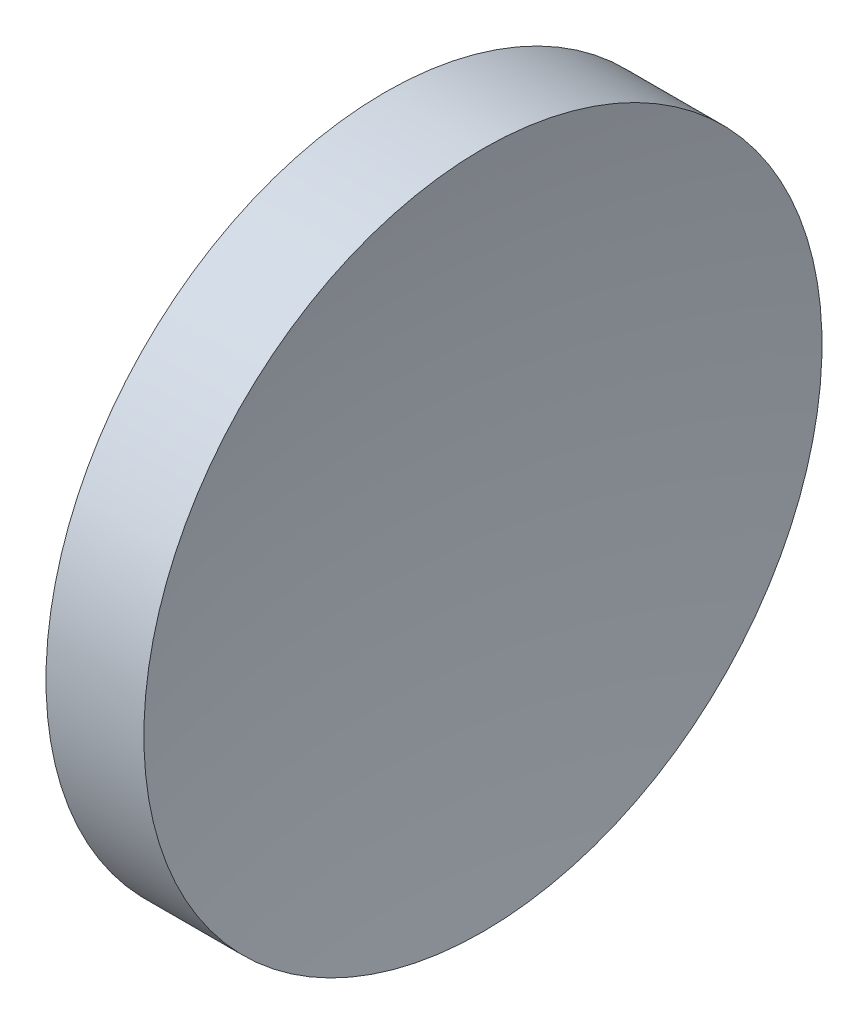
SolidWorks part; units mm, degrees
ref_plane "前视基准面" through (0, 0, 0) normal (0, 0, 1) x (1, 0, 0)
ref_plane "上视基准面" through (0, 0, 0) normal (0, 1, 0) x (1, 0, 0)
ref_plane "右视基准面" through (0, 0, 0) normal (1, 0, 0) x (0, 0, -1)
sketch "草图1" plane through (0, 0, 0) normal (0, 0, 1) x (1, 0, 0)
  line L0 (110.0148, 65.1575) -> (128.1887, 65.1575) construction
  line L1 (114.9862, 65.1575) -> (114.9862, 82.1575)
  line L2 (114.9862, 82.1575) -> (119.8938, 82.1575)
  line L3 (118.2362, 65.1575) -> (114.9862, 65.1575)
  arc A0 (119.8938, 82.1575) -> (118.2362, 65.1575) centre (206.2362, 65.1575) ccw
revolve "旋转1" add sketch "草图1" angle 360 about L0
